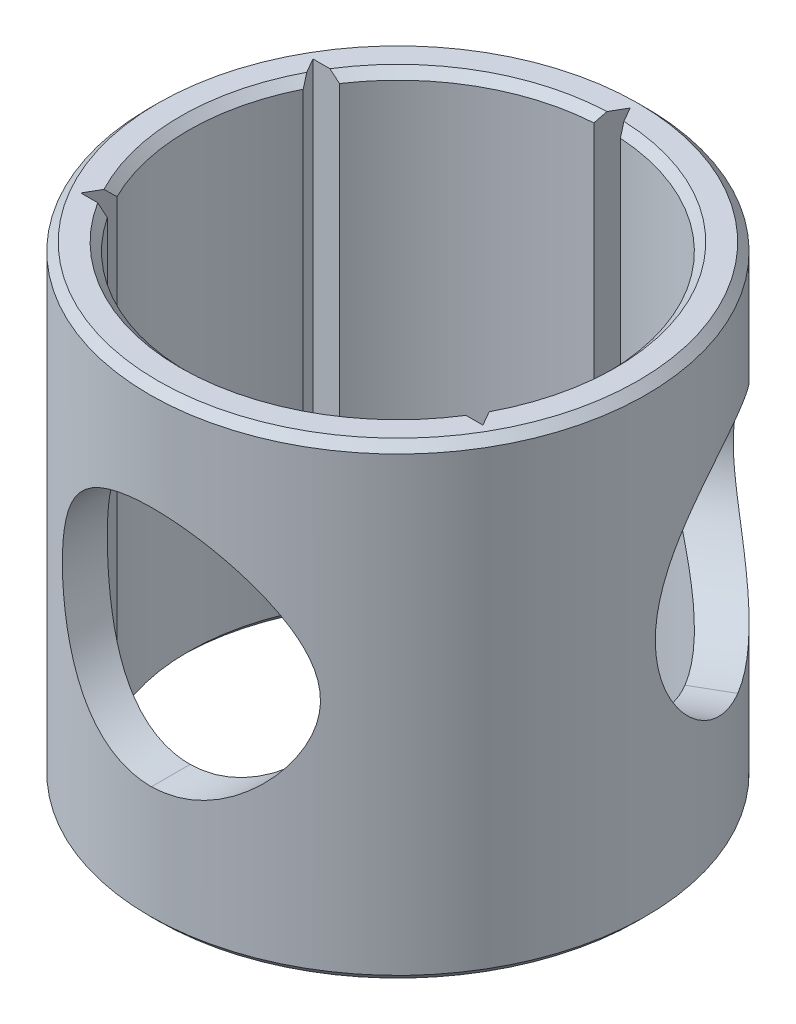
SolidWorks part; units mm, degrees
ref_plane "Ebene vorne" through (0, 0, 0) normal (0, 0, 1) x (1, 0, 0)
ref_plane "Ebene oben" through (0, 0, 0) normal (0, 1, 0) x (1, 0, 0)
ref_plane "Ebene rechts" through (0, 0, 0) normal (1, 0, 0) x (0, 0, -1)
sketch "Skizze1" plane through (0, 0, 0) normal (0, 1, 0) x (1, 0, 0)
  circle A0 centre (0, 0) radius 13
  circle A1 centre (0, 0) radius 15.4
  dimension "D1" = 26
  dimension "D2" = 30.8
extrude "Aufsatz-Linear austragen1" add sketch "Skizze1" along normal blind 29
sketch "Skizze2" plane through (0, 29, 0) normal (0, 1, 0) x (1, 0, 0)
  line L1 (0, 14.4) -> (-1.2124, 12.3)
  line L2 (-1.2124, 12.3) -> (1.2124, 12.3)
  line L3 (1.2124, 12.3) -> (0, 14.4)
  circle A0 centre (0, 13) radius 0.7 construction
  circle A1 centre (0, 0) radius 13 construction
  dimension "D1" = 1.4
extrude "Schnitt-Linear austragen1" cut sketch "Skizze2" against normal blind 30
pattern_circular "Kreismuster1" count 6 over 360 about axis through (0, 0, 0) along (0, 1, 0) skipping 3, 5 of "Schnitt-Linear austragen1"
sketch3d "3D-Skizze1"
  spline S0 degree 3 poles (-457.6373, -1653.7984, -975.9731) (-97.1864, -142.0144, -82.2273) (-28.6155, 28.5725, 16.7947) (2.1671, 22.2371, 12.8282) (2.6665, 22.0809, 12.7328) (3.606, 21.6883, 12.4992) (4.0502, 21.4519, 12.3611) (4.8934, 20.905, 12.0522) (5.2851, 20.5992, 11.884) (5.8276, 20.0999, 11.6224) (6.0012, 19.9264, 11.5335) (6.3344, 19.5649, 11.3539) (6.4946, 19.3761, 11.2628) (6.9484, 18.793, 10.9929) (7.2167, 18.3823, 10.8166) (7.6782, 17.5043, 10.494) (7.8731, 17.0307, 10.3462) (8.0761, 16.2899, 10.1874) (8.1293, 16.0372, 10.1448) (8.2016, 15.518, 10.0864) (8.2199, 15.2544, 10.0714) (8.2194, 14.7336, 10.0718) (8.2008, 14.4742, 10.0871) (8.1282, 13.9574, 10.1456) (8.0739, 13.7007, 10.1892) (7.9379, 13.2073, 10.2955) (7.8559, 12.9679, 10.3585) (7.6677, 12.5009, 10.4986) (7.5609, 12.2722, 10.576) (7.2118, 11.6092, 10.8199) (6.9431, 11.1997, 10.9962) (6.4929, 10.6219, 11.2638) (6.3348, 10.4355, 11.3537) (6.0022, 10.0747, 11.5329) (5.827, 9.8995, 11.6227) (5.2817, 9.3979, 11.8855) (4.8933, 9.0954, 12.052) (4.2697, 8.6903, 12.2808) (4.055, 8.5635, 12.3536) (3.6106, 8.3272, 12.4907) (3.3796, 8.2174, 12.5554) (2.6708, 7.9203, 12.732) (2.1818, 7.7668, 12.8258) (-21.2275, 2.9072, 15.8664) (-86.0881, 98.182, -39.1961) (1664.0012, 951.8719, -559.7226) knots -3.679496 -3.679496 -3.679496 -3.679496 0.0625 0.0625 0.125 0.125 0.1875 0.1875 0.25 0.25 0.28125 0.28125 0.3125 0.3125 0.375 0.375 0.4375 0.4375 0.46875 0.46875 0.5 0.5 0.53125 0.53125 0.5625 0.5625 0.59375 0.59375 0.625 0.625 0.6875 0.6875 0.71875 0.71875 0.75 0.75 0.8125 0.8125 0.84375 0.84375 0.875 0.875 0.9375 0.9375 3.759159 3.759159 3.759159 3.759159 only from (0.1111, 22.5, 12.9995) to (0.1111, 7.5, 12.9995) construction
  spline S1 degree 3 poles (0.1111, 22.5, 12.9995) (0.6393, 22.5, 12.995) (1.1557, 22.4452, 12.9586) (2.1671, 22.2371, 12.8282) (2.6665, 22.0809, 12.7328) (3.606, 21.6883, 12.4992) (4.0502, 21.4519, 12.3611) (4.8934, 20.905, 12.0522) (5.2851, 20.5992, 11.884) (5.8276, 20.0999, 11.6224) (6.0012, 19.9264, 11.5335) (6.3344, 19.5649, 11.3539) (6.4946, 19.3761, 11.2628) (6.9484, 18.793, 10.9929) (7.2167, 18.3823, 10.8166) (7.6782, 17.5043, 10.494) (7.8731, 17.0307, 10.3462) (8.0761, 16.2899, 10.1874) (8.1293, 16.0372, 10.1448) (8.2016, 15.518, 10.0864) (8.2199, 15.2544, 10.0714) (8.2194, 14.7336, 10.0718) (8.2008, 14.4742, 10.0871) (8.1282, 13.9574, 10.1456) (8.0739, 13.7007, 10.1892) (7.9379, 13.2073, 10.2955) (7.8559, 12.9679, 10.3585) (7.6677, 12.5009, 10.4986) (7.5609, 12.2722, 10.576) (7.2118, 11.6092, 10.8199) (6.9431, 11.1997, 10.9962) (6.4929, 10.6219, 11.2638) (6.3348, 10.4355, 11.3537) (6.0022, 10.0747, 11.5329) (5.827, 9.8995, 11.6227) (5.2817, 9.3979, 11.8855) (4.8933, 9.0954, 12.052) (4.2697, 8.6903, 12.2808) (4.055, 8.5635, 12.3536) (3.6106, 8.3272, 12.4907) (3.3796, 8.2174, 12.5554) (2.6708, 7.9203, 12.732) (2.1818, 7.7668, 12.8258) (1.1672, 7.5562, 12.9576) (0.6393, 7.5, 12.995) (0.1111, 7.5, 12.9995) knots 0 0 0 0 0.0625 0.0625 0.125 0.125 0.1875 0.1875 0.25 0.25 0.28125 0.28125 0.3125 0.3125 0.375 0.375 0.4375 0.4375 0.46875 0.46875 0.5 0.5 0.53125 0.53125 0.5625 0.5625 0.59375 0.59375 0.625 0.625 0.6875 0.6875 0.71875 0.71875 0.75 0.75 0.8125 0.8125 0.84375 0.84375 0.875 0.875 0.9375 0.9375 1 1 1 1
  spline S2 degree 3 poles (419.1015, 1299.7716, -1451.6243) (117.6658, 245.0229, -117.1146) (33.5692, 0.596, 16.6152) (-1.8468, 7.7441, 12.8773) (-2.3241, 7.8921, 12.7988) (-3.2185, 8.2722, 12.6036) (-3.6402, 8.5042, 12.4869) (-4.4351, 9.0532, 12.2272) (-4.798, 9.3633, 12.0875) (-5.2909, 9.8768, 11.8759) (-5.4469, 10.0564, 11.805) (-5.7423, 10.4328, 11.6642) (-5.8813, 10.6296, 11.5944) (-6.2658, 11.2344, 11.394) (-6.4819, 11.6606, 11.2706) (-6.7472, 12.3371, 11.1124) (-6.8261, 12.5701, 11.064) (-6.9613, 13.0431, 10.9794) (-7.0175, 13.2818, 10.9434) (-7.1527, 14.0042, 10.8559) (-7.1989, 14.4944, 10.8248) (-7.1994, 15.2434, 10.8244) (-7.1879, 15.4941, 10.8321) (-7.1425, 15.9872, 10.8621) (-7.0746, 16.475, 10.9068) (-6.9624, 16.9526, 10.9787) (-6.8276, 17.4251, 11.063) (-6.7487, 17.6588, 11.1115) (-6.483, 18.3373, 11.27) (-6.2663, 18.765, 11.3938) (-5.8802, 19.3721, 11.595) (-5.7408, 19.5692, 11.6649) (-5.4462, 19.9444, 11.8053) (-5.2906, 20.1235, 11.8761) (-4.7984, 20.6363, 12.0873) (-4.4352, 20.9467, 12.2272) (-3.6407, 21.4955, 12.4868) (-3.2201, 21.7268, 12.6031) (-2.5528, 22.0109, 12.7489) (-2.3242, 22.095, 12.7928) (-1.8541, 22.2411, 12.8693) (-1.6121, 22.3031, 12.902) (36.2667, 29.9756, 16.9146) (123.0672, -256.026, -139.4864) (372.8421, -1147.1035, -1560.664) knots -4.464251 -4.464251 -4.464251 -4.464251 0.0625 0.0625 0.125 0.125 0.1875 0.1875 0.25 0.25 0.28125 0.28125 0.3125 0.3125 0.375 0.375 0.40625 0.40625 0.4375 0.4375 0.5 0.5 0.53125 0.53125 0.5625 0.59375 0.59375 0.625 0.625 0.6875 0.6875 0.71875 0.71875 0.75 0.75 0.8125 0.8125 0.875 0.875 0.90625 0.90625 0.9375 0.9375 5.784955 5.784955 5.784955 5.784955 only from (0.1111, 7.5, 12.9995) to (0.1111, 22.5, 12.9995) construction
  spline S3 degree 3 poles (0.1111, 7.5, 12.9995) (-0.3904, 7.5, 13.0038) (-0.8821, 7.5494, 12.9791) (-1.8468, 7.7441, 12.8773) (-2.3241, 7.8921, 12.7988) (-3.2185, 8.2722, 12.6036) (-3.6402, 8.5042, 12.4869) (-4.4351, 9.0532, 12.2272) (-4.798, 9.3633, 12.0875) (-5.2909, 9.8768, 11.8759) (-5.4469, 10.0564, 11.805) (-5.7423, 10.4328, 11.6642) (-5.8813, 10.6296, 11.5944) (-6.2658, 11.2344, 11.394) (-6.4819, 11.6606, 11.2706) (-6.7472, 12.3371, 11.1124) (-6.8261, 12.5701, 11.064) (-6.9613, 13.0431, 10.9794) (-7.0175, 13.2818, 10.9434) (-7.1527, 14.0042, 10.8559) (-7.1989, 14.4944, 10.8248) (-7.1994, 15.2434, 10.8244) (-7.1879, 15.4941, 10.8321) (-7.1425, 15.9872, 10.8621) (-7.0746, 16.475, 10.9068) (-6.9624, 16.9526, 10.9787) (-6.8276, 17.4251, 11.063) (-6.7487, 17.6588, 11.1115) (-6.483, 18.3373, 11.27) (-6.2663, 18.765, 11.3938) (-5.8802, 19.3721, 11.595) (-5.7408, 19.5692, 11.6649) (-5.4462, 19.9444, 11.8053) (-5.2906, 20.1235, 11.8761) (-4.7984, 20.6363, 12.0873) (-4.4352, 20.9467, 12.2272) (-3.6407, 21.4955, 12.4868) (-3.2201, 21.7268, 12.6031) (-2.5528, 22.0109, 12.7489) (-2.3242, 22.095, 12.7928) (-1.8541, 22.2411, 12.8693) (-1.6121, 22.3031, 12.902) (-0.8842, 22.4505, 12.9791) (-0.3908, 22.5, 13.0038) (0.1111, 22.5, 12.9995) knots 0 0 0 0 0.0625 0.0625 0.125 0.125 0.1875 0.1875 0.25 0.25 0.28125 0.28125 0.3125 0.3125 0.375 0.375 0.40625 0.40625 0.4375 0.4375 0.5 0.5 0.53125 0.53125 0.5625 0.59375 0.59375 0.625 0.625 0.6875 0.6875 0.71875 0.71875 0.75 0.75 0.8125 0.8125 0.875 0.875 0.90625 0.90625 0.9375 0.9375 1 1 1 1
sketch "Skizze4" plane through (0, 0, 0) normal (0, 0, 1) x (1, 0, 0)
  spline S0 degree 3 poles (-518.1127, -1908.464) (-104.6424, -160.7971) (-30.2373, 28.9063) (2.1671, 22.2371) (2.6665, 22.0809) (3.606, 21.6883) (4.0502, 21.4519) (4.8934, 20.905) (5.2851, 20.5992) (5.8276, 20.0999) (6.0012, 19.9264) (6.3344, 19.5649) (6.4946, 19.3761) (6.9484, 18.793) (7.2167, 18.3823) (7.6782, 17.5043) (7.8731, 17.0307) (8.0761, 16.2899) (8.1293, 16.0372) (8.2016, 15.518) (8.2199, 15.2544) (8.2194, 14.7336) (8.2008, 14.4742) (8.1282, 13.9574) (8.0739, 13.7007) (7.9379, 13.2073) (7.8559, 12.9679) (7.6677, 12.5009) (7.5609, 12.2722) (7.2118, 11.6092) (6.9431, 11.1997) (6.4929, 10.6219) (6.3348, 10.4355) (6.0022, 10.0747) (5.827, 9.8995) (5.2817, 9.3979) (4.8933, 9.0954) (4.2697, 8.6903) (4.055, 8.5635) (3.6106, 8.3272) (3.3796, 8.2174) (2.6708, 7.9203) (2.1818, 7.7668) (-21.5542, 2.8394) (-87.9467, 100.9199) (1739.992, 988.8619) knots -3.879941 -3.879941 -3.879941 -3.879941 0.0625 0.0625 0.125 0.125 0.1875 0.1875 0.25 0.25 0.28125 0.28125 0.3125 0.3125 0.375 0.375 0.4375 0.4375 0.46875 0.46875 0.5 0.5 0.53125 0.53125 0.5625 0.5625 0.59375 0.59375 0.625 0.625 0.6875 0.6875 0.71875 0.71875 0.75 0.75 0.8125 0.8125 0.84375 0.84375 0.875 0.875 0.9375 0.9375 3.799401 3.799401 3.799401 3.799401 only from (0.1111, 22.5) to (0.1111, 7.5) construction
  spline S1 degree 3 poles (0.1111, 22.5) (0.6393, 22.5) (1.1557, 22.4452) (2.1671, 22.2371) (2.6665, 22.0809) (3.606, 21.6883) (4.0502, 21.4519) (4.8934, 20.905) (5.2851, 20.5992) (5.8276, 20.0999) (6.0012, 19.9264) (6.3344, 19.5649) (6.4946, 19.3761) (6.9484, 18.793) (7.2167, 18.3823) (7.6782, 17.5043) (7.8731, 17.0307) (8.0761, 16.2899) (8.1293, 16.0372) (8.2016, 15.518) (8.2199, 15.2544) (8.2194, 14.7336) (8.2008, 14.4742) (8.1282, 13.9574) (8.0739, 13.7007) (7.9379, 13.2073) (7.8559, 12.9679) (7.6677, 12.5009) (7.5609, 12.2722) (7.2118, 11.6092) (6.9431, 11.1997) (6.4929, 10.6219) (6.3348, 10.4355) (6.0022, 10.0747) (5.827, 9.8995) (5.2817, 9.3979) (4.8933, 9.0954) (4.2697, 8.6903) (4.055, 8.5635) (3.6106, 8.3272) (3.3796, 8.2174) (2.6708, 7.9203) (2.1818, 7.7668) (1.1672, 7.5562) (0.6393, 7.5) (0.1111, 7.5) knots 0 0 0 0 0.0625 0.0625 0.125 0.125 0.1875 0.1875 0.25 0.25 0.28125 0.28125 0.3125 0.3125 0.375 0.375 0.4375 0.4375 0.46875 0.46875 0.5 0.5 0.53125 0.53125 0.5625 0.5625 0.59375 0.59375 0.625 0.625 0.6875 0.6875 0.71875 0.71875 0.75 0.75 0.8125 0.8125 0.84375 0.84375 0.875 0.875 0.9375 0.9375 1 1 1 1
  spline S2 degree 3 poles (594.1635, 1916.5736) (147.9485, 336.2315) (39.5587, -0.6129) (-1.8468, 7.7441) (-2.3241, 7.8921) (-3.2185, 8.2722) (-3.6402, 8.5042) (-4.4351, 9.0532) (-4.798, 9.3633) (-5.2909, 9.8768) (-5.4469, 10.0564) (-5.7423, 10.4328) (-5.8813, 10.6296) (-6.2658, 11.2344) (-6.4819, 11.6606) (-6.7472, 12.3371) (-6.8261, 12.5701) (-6.9613, 13.0431) (-7.0175, 13.2818) (-7.1527, 14.0042) (-7.1989, 14.4944) (-7.1994, 15.2434) (-7.1879, 15.4941) (-7.1425, 15.9872) (-7.0746, 16.475) (-6.9624, 16.9526) (-6.8276, 17.4251) (-6.7487, 17.6588) (-6.483, 18.3373) (-6.2663, 18.765) (-5.8802, 19.3721) (-5.7408, 19.5692) (-5.4462, 19.9444) (-5.2906, 20.1235) (-4.7984, 20.6363) (-4.4352, 20.9467) (-3.6407, 21.4955) (-3.2201, 21.7268) (-2.5528, 22.0109) (-2.3242, 22.095) (-1.8541, 22.2411) (-1.6121, 22.3031) (45.2292, 31.791) (167.1955, -408.8905) (580.5448, -1890.8355) knots -5.240382 -5.240382 -5.240382 -5.240382 0.0625 0.0625 0.125 0.125 0.1875 0.1875 0.25 0.25 0.28125 0.28125 0.3125 0.3125 0.375 0.375 0.40625 0.40625 0.4375 0.4375 0.5 0.5 0.53125 0.53125 0.5625 0.59375 0.59375 0.625 0.625 0.6875 0.6875 0.71875 0.71875 0.75 0.75 0.8125 0.8125 0.875 0.875 0.90625 0.90625 0.9375 0.9375 6.9393 6.9393 6.9393 6.9393 only from (0.1111, 7.5) to (0.1111, 22.5) construction
  spline S3 degree 3 poles (0.1111, 7.5) (-0.3904, 7.5) (-0.8821, 7.5494) (-1.8468, 7.7441) (-2.3241, 7.8921) (-3.2185, 8.2722) (-3.6402, 8.5042) (-4.4351, 9.0532) (-4.798, 9.3633) (-5.2909, 9.8768) (-5.4469, 10.0564) (-5.7423, 10.4328) (-5.8813, 10.6296) (-6.2658, 11.2344) (-6.4819, 11.6606) (-6.7472, 12.3371) (-6.8261, 12.5701) (-6.9613, 13.0431) (-7.0175, 13.2818) (-7.1527, 14.0042) (-7.1989, 14.4944) (-7.1994, 15.2434) (-7.1879, 15.4941) (-7.1425, 15.9872) (-7.0746, 16.475) (-6.9624, 16.9526) (-6.8276, 17.4251) (-6.7487, 17.6588) (-6.483, 18.3373) (-6.2663, 18.765) (-5.8802, 19.3721) (-5.7408, 19.5692) (-5.4462, 19.9444) (-5.2906, 20.1235) (-4.7984, 20.6363) (-4.4352, 20.9467) (-3.6407, 21.4955) (-3.2201, 21.7268) (-2.5528, 22.0109) (-2.3242, 22.095) (-1.8541, 22.2411) (-1.6121, 22.3031) (-0.8842, 22.4505) (-0.3908, 22.5) (0.1111, 22.5) knots 0 0 0 0 0.0625 0.0625 0.125 0.125 0.1875 0.1875 0.25 0.25 0.28125 0.28125 0.3125 0.3125 0.375 0.375 0.40625 0.40625 0.4375 0.4375 0.5 0.5 0.53125 0.53125 0.5625 0.59375 0.59375 0.625 0.625 0.6875 0.6875 0.71875 0.71875 0.75 0.75 0.8125 0.8125 0.875 0.875 0.90625 0.90625 0.9375 0.9375 1 1 1 1
extrude "Schnitt-Linear austragen2" cut sketch "Skizze4" along normal blind 40
pattern_circular "Kreismuster2" count 2 every 120 about axis through (0, 29, 0) along (0, 1, 0) of "Schnitt-Linear austragen2"
chamfer "Fase1" distance 0.5 angle 45 10 edges at (0, 0, 13) (-13, 0, 0) (-6.5, 0, -11.2583) (11.2583, 0, -6.5) (11.2583, 29, -6.5) (-6.5, 29, -11.2583) (-13, 29, 0) (0, 29, 13) (0, 0, 15.4) (0, 29, 15.4)
